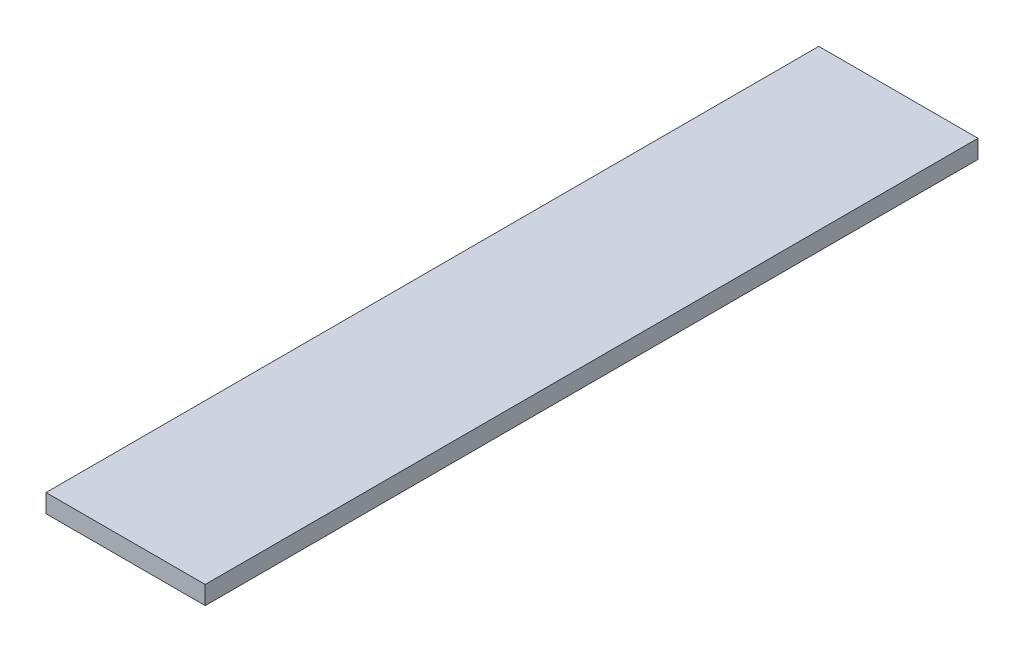
SolidWorks part; units mm, degrees
material "Balsa"
ref_plane "Alzado" through (0, 0, 0) normal (0, 0, 1) x (1, 0, 0)
ref_plane "Planta" through (0, 0, 0) normal (0, 1, 0) x (1, 0, 0)
ref_plane "Vista lateral" through (0, 0, 0) normal (1, 0, 0) x (0, 0, -1)
sketch "Croquis1" plane through (0, 0, 0) normal (0, 1, 0) x (1, 0, 0)
  line L1 (0, 0) -> (26, 0)
  line L2 (0, 0) -> (0, 126.2)
  line L3 (0, 126.2) -> (26, 126.2)
  line L4 (26, 0) -> (26, 126.2)
extrude "Saliente-Extruir1" add sketch "Croquis1" along normal blind 3
